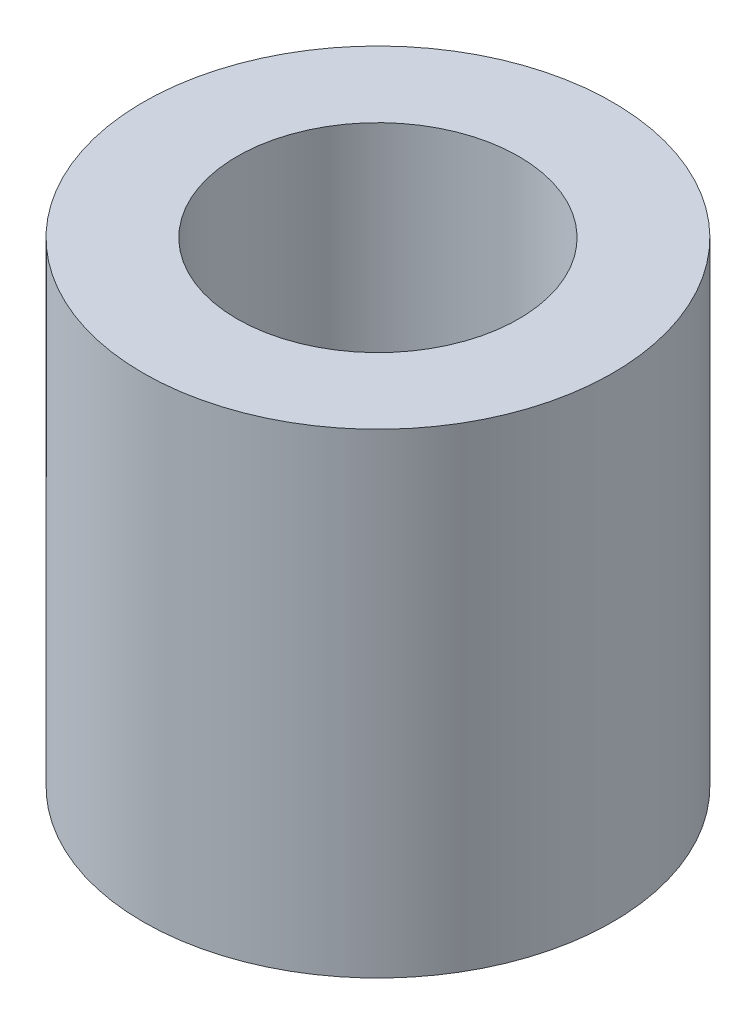
SolidWorks part; units mm, degrees
ref_plane "Front Plane" through (0, 0, 0) normal (0, 0, 1) x (1, 0, 0)
ref_plane "Top Plane" through (0, 0, 0) normal (0, 1, 0) x (1, 0, 0)
ref_plane "Right Plane" through (0, 0, 0) normal (1, 0, 0) x (0, 0, -1)
sketch "Sketch1" plane through (0, 0, 0) normal (0, 1, 0) x (1, 0, 0)
  circle A0 centre (0, 0) radius 2.667
  circle A1 centre (0, 0) radius 4.445
  dimension "D1" = 5.334
  dimension "D2" = 8.89
extrude "Boss-Extrude1" add sketch "Sketch1" along normal blind 9
